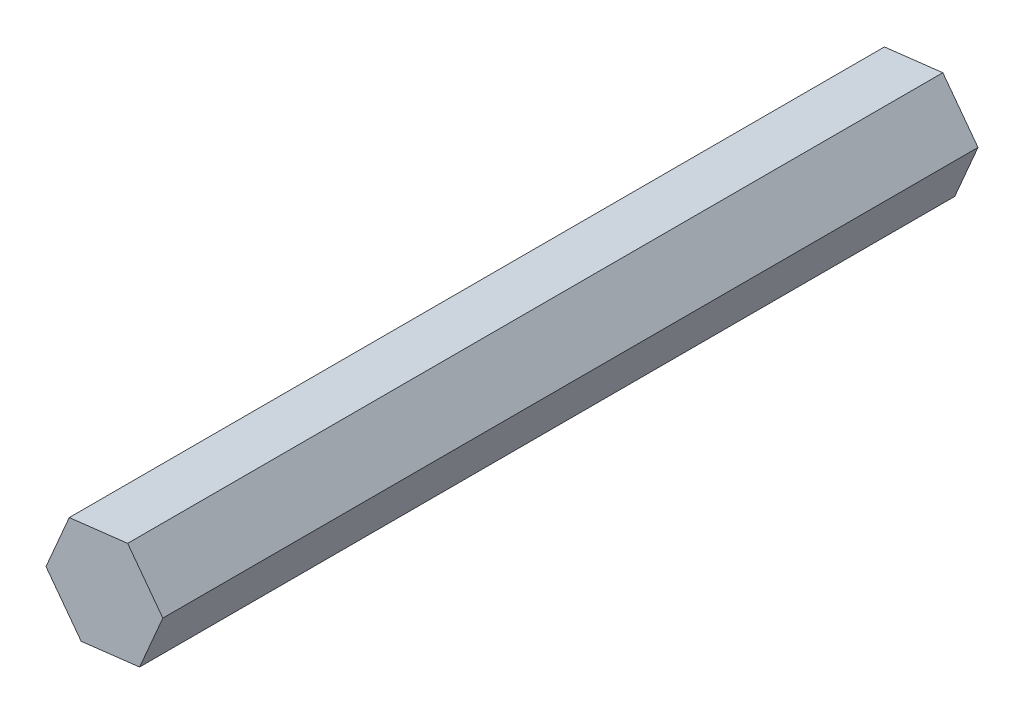
SolidWorks part; units mm, degrees
ref_plane "Front Plane" through (0, 0, 0) normal (0, 0, 1) x (1, 0, 0)
ref_plane "Top Plane" through (0, 0, 0) normal (0, 1, 0) x (1, 0, 0)
ref_plane "Right Plane" through (0, 0, 0) normal (1, 0, 0) x (0, 0, -1)
sketch "Sketch1" plane through (0, 0, 0) normal (0, 0, 1) x (1, 0, 0)
  line L0 (0, 0) -> (-0.7431, 6.3064) construction
  line L1 (-7.282, -0.8581) -> (-2.8979, -6.7354)
  line L2 (-2.8979, -6.7354) -> (4.3841, -5.8773)
  line L3 (4.3841, -5.8773) -> (7.282, 0.8581)
  line L4 (7.282, 0.8581) -> (2.8979, 6.7354)
  line L5 (2.8979, 6.7354) -> (-4.3841, 5.8773)
  line L6 (-4.3841, 5.8773) -> (-7.282, -0.8581)
  line L7 (0, 0) -> (7.282, 0.8581) construction
  circle A0 centre (0, 0) radius 6.35 construction
  dimension "D1" = 12.7
  dimension "D2" = 7.282
extrude "Boss-Extrude1" add sketch "Sketch1" along normal blind 101.6
